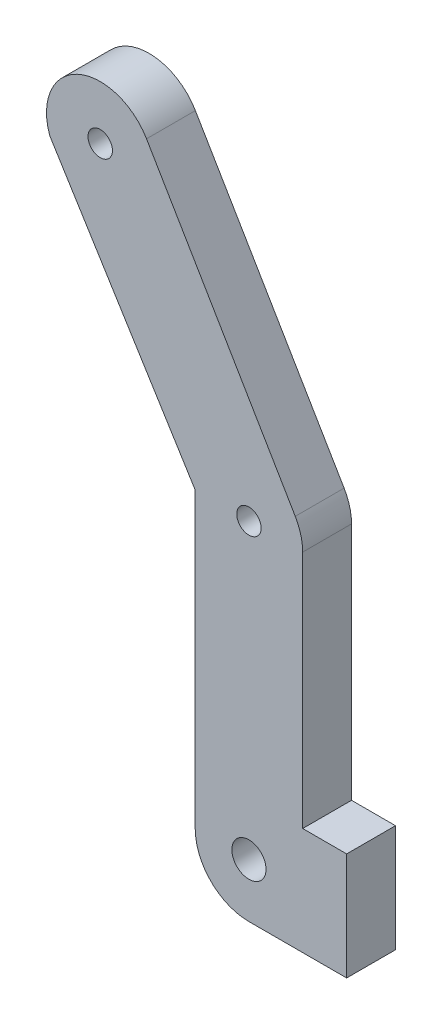
SolidWorks part; units mm, degrees
ref_plane "Front Plane" through (0, 0, 0) normal (0, 0, 1) x (1, 0, 0)
ref_plane "Top Plane" through (0, 0, 0) normal (0, 1, 0) x (1, 0, 0)
ref_plane "Right Plane" through (0, 0, 0) normal (1, 0, 0) x (0, 0, -1)
sketch "Sketch1" plane through (0, 0, 0) normal (0, 0, 1) x (1, 0, 0)
  line L0 (274.7357, 378.6909) -> (274.7357, 354.1909)
  line L1 (279.2357, 354.1909) -> (279.2357, 343.1909)
  line L2 (279.2357, 343.1909) -> (269.2357, 343.1909)
  line L3 (274.7357, 354.1909) -> (279.2357, 354.1909)
  line L4 (263.7357, 348.6909) -> (263.7357, 378.6909)
  line L5 (263.7357, 378.6909) -> (248.8498, 402.65)
  line L6 (258.7535, 407.3331) -> (273.9751, 381.4815)
  circle A0 centre (254.014, 404.5424) radius 1.25
  circle A1 centre (269.2357, 378.6909) radius 1.25
  circle A2 centre (269.2357, 348.6909) radius 1.75
  arc A3 (274.7357, 378.6909) -> (273.9751, 381.4815) centre (269.2357, 378.6909) ccw
  arc A4 (263.7357, 348.6909) -> (269.2357, 343.1909) centre (269.2357, 348.6909) ccw
  arc A5 (258.7535, 407.3331) -> (250.0297, 400.7509) centre (254.014, 404.5424) ccw
  dimension "D2" = 2.5
  dimension "D1" = 30
  dimension "D3" = 11
  dimension "D4" = 10
extrude "Boss-Extrude1" add sketch "Sketch1" along normal blind 5 contours L6 A5 L5 L4 A4 L2 L1 L3 L0 A3 A0 A1 A2
